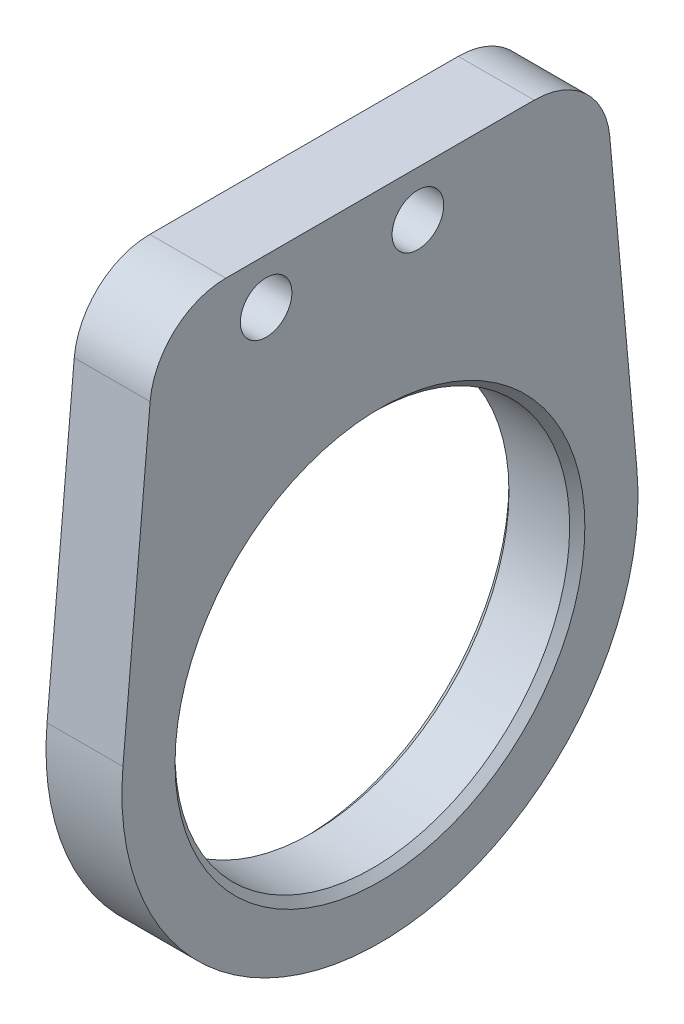
SolidWorks part; units mm, degrees
ref_plane "前视基准面" through (0, 0, 0) normal (0, 0, 1) x (1, 0, 0)
ref_plane "上视基准面" through (0, 0, 0) normal (0, 1, 0) x (1, 0, 0)
ref_plane "右视基准面" through (0, 0, 0) normal (1, 0, 0) x (0, 0, -1)
other "Configuration Table"
sketch "草图1" plane through (0, 0, 0) normal (1, 0, 0) x (0, 0, -1)
  line L0 (-15, 23) -> (15, 23)
  line L1 (-15, 23) -> (-16.9317, 1.5228)
  line L2 (15, 23) -> (16.9317, 1.5228)
  line L3 (-15, 23) -> (-15, 26)
  line L4 (-15, 26) -> (15, 26)
  line L5 (15, 26) -> (15, 23)
  circle A0 centre (0, 0) radius 13
  circle A1 centre (0, 0) radius 17
  dimension "D1" = 26
  dimension "D2" = 34
  dimension "D3" = 23
  dimension "D4" = 30
  dimension "D5" = 15
  dimension "D6" = 3
extrude "凸台-拉伸1" add sketch "草图1" along normal blind 5 contours A1 A0 | A1 L2 L0 L1 | L5 L4 L3 L0
fillet "圆角1" radius 5 2 edges at (2.5, 26, 15) (2.5, 26, -15)
hole_wizard "M3 间隙孔1" positions "草图2" profile "草图3" hole size "M3" standard "GB" end condition through all
sketch "草图2" plane through (0, 0, 0) normal (-1, 0, 0) x (0, 0, 1)
  line L0 (10.1597, 26) -> (-10.1597, 26) construction
  point P0 (-2.5, 23)
  point P3 (7.5, 23)
  dimension "D1" = 9.4317
  dimension "D2" = 19.4317
  dimension "D3" = 3
sketch "草图3" plane through (0, 23, -2.5) normal (0, 1, 0) x (0, 0, 1)
  line L0 (0, 0) -> (0, 5)
  line L1 (0, 5) -> (1.7, 5)
  line L2 (1.7, 5) -> (1.7, 0)
  line L5 (1.7, 0) -> (0, 0)
  line L11 (0, -6.35) -> (0, 107.95) construction
  dimension "通孔孔直径" = 3.4
  dimension "通孔孔深度" = 5
chamfer "Chamfer1" distance 0.5 angle 45 2 edges at (0, 0, -13) (5, 0, -13)
